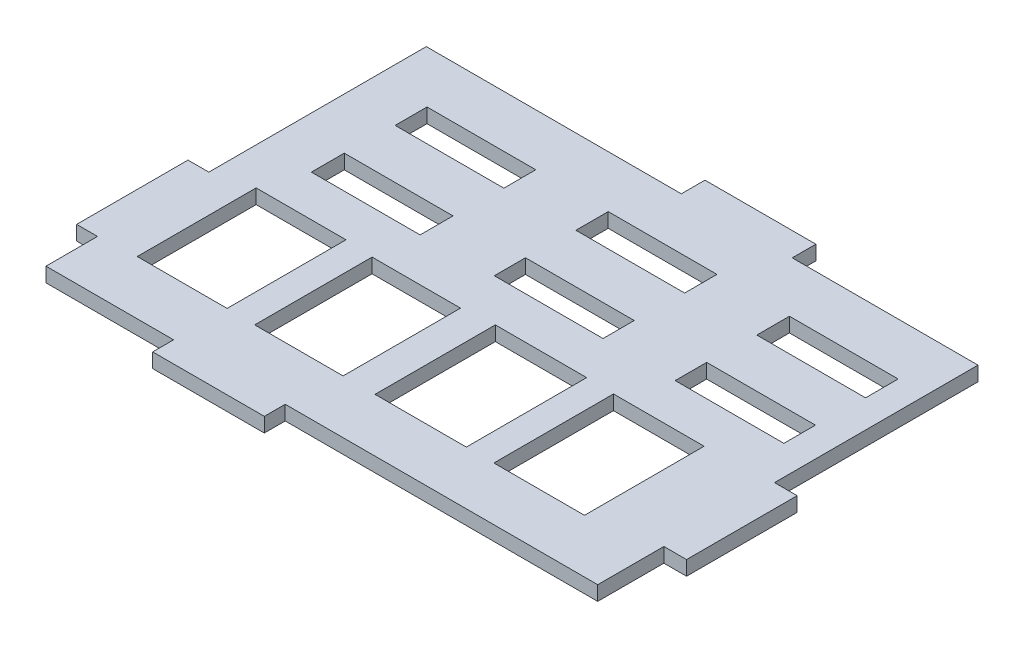
SolidWorks part; units mm, degrees
ref_plane "Front Plane" through (0, 0, 0) normal (0, 0, 1) x (1, 0, 0)
ref_plane "Top Plane" through (0, 0, 0) normal (0, 1, 0) x (1, 0, 0)
ref_plane "Right Plane" through (0, 0, 0) normal (1, 0, 0) x (0, 0, -1)
sketch "Sketch1" plane through (0, 0, 0) normal (0, 1, 0) x (1, 0, 0)
  line L0 (56.9516, 84.2137) -> (56.9516, 75.1881)
  line L1 (56.9516, 141.8209) -> (56.9516, 134.5917)
  line L2 (65.9326, 112.7049) -> (65.9326, 118.4707)
  line L3 (56.9516, 75.1881) -> (79.3066, 75.1881)
  line L4 (153.6179, 141.8209) -> (153.6179, 106.1651)
  line L5 (65.9326, 112.7049) -> (84.9826, 112.7049)
  line L6 (84.9826, 112.7049) -> (84.9826, 118.4707)
  line L7 (65.9326, 118.4707) -> (84.9826, 118.4707)
  line L8 (129.4326, 112.9462) -> (129.4326, 118.4707)
  line L9 (129.4326, 112.9462) -> (148.4826, 112.9462)
  line L10 (148.4826, 112.9462) -> (148.4826, 118.4707)
  line L11 (129.4326, 118.4707) -> (148.4826, 118.4707)
  line L12 (97.6826, 113.0097) -> (97.6826, 118.4707)
  line L13 (97.6826, 113.0097) -> (116.7326, 113.0097)
  line L14 (116.7326, 113.0097) -> (116.7326, 118.4707)
  line L15 (97.6826, 118.4707) -> (116.7326, 118.4707)
  line L16 (56.9516, 116.0497) -> (56.9516, 103.7209)
  line L17 (56.9516, 134.5917) -> (56.9539, 134.5917)
  line L18 (98.8646, 75.1881) -> (153.6179, 75.1881)
  line L19 (56.9516, 116.0497) -> (56.9539, 116.0497)
  line L20 (56.9539, 134.5917) -> (56.9539, 116.0497)
  line L21 (153.6179, 86.7849) -> (153.6179, 75.1881)
  line L22 (79.3066, 75.1881) -> (79.3066, 71.5259)
  line L23 (79.3066, 71.5259) -> (98.8646, 71.5259)
  line L24 (98.8646, 75.1881) -> (98.8646, 71.5259)
  line L25 (153.6179, 106.1651) -> (157.5853, 106.1651)
  line L26 (121.0628, 141.8209) -> (153.6179, 141.8209)
  line L27 (153.6179, 86.7849) -> (157.5853, 86.7849)
  line L28 (157.5853, 106.1651) -> (157.5853, 86.7849)
  line L30 (101.6318, 141.8209) -> (101.6318, 145.9673)
  line L31 (101.6318, 145.9673) -> (121.0628, 145.9673)
  line L32 (121.0628, 141.8209) -> (121.0628, 145.9673)
  line L33 (63.4844, 105.472) -> (79.2324, 105.472)
  line L34 (63.4844, 105.472) -> (63.4844, 84.644)
  line L35 (63.4844, 84.644) -> (79.2324, 84.644)
  line L36 (79.2324, 105.472) -> (79.2324, 84.644)
  line L37 (84.1413, 105.132) -> (99.6353, 105.132)
  line L38 (84.1413, 105.132) -> (84.1413, 84.558)
  line L39 (84.1413, 84.558) -> (99.6353, 84.558)
  line L40 (99.6353, 105.132) -> (99.6353, 84.558)
  line L41 (105.2285, 105.64) -> (121.2305, 105.64)
  line L42 (105.2285, 105.64) -> (105.2285, 84.558)
  line L43 (105.2285, 84.558) -> (121.2305, 84.558)
  line L44 (121.2305, 105.64) -> (121.2305, 84.558)
  line L45 (126.0575, 105.513) -> (141.9325, 105.513)
  line L46 (126.0575, 105.513) -> (126.0575, 84.558)
  line L47 (126.0575, 84.558) -> (141.9325, 84.558)
  line L48 (141.9325, 105.513) -> (141.9325, 84.558)
  line L61 (56.9516, 141.8209) -> (101.6318, 141.8209)
  line L62 (53.2966, 103.7209) -> (53.2966, 84.2137)
  line L65 (53.2966, 103.7209) -> (56.9516, 103.7209)
  line L69 (53.2966, 84.2137) -> (56.9516, 84.2137)
  line L85 (66.178, 127.1328) -> (66.178, 132.7208)
  line L89 (66.178, 127.1328) -> (85.228, 127.1328)
  line L92 (85.228, 127.1328) -> (85.228, 132.7208)
  line L97 (66.178, 132.7208) -> (85.228, 132.7208)
  line L100 (129.678, 127.0058) -> (129.678, 132.7208)
  line L101 (129.678, 127.0058) -> (148.728, 127.0058)
  line L102 (148.728, 127.0058) -> (148.728, 132.7208)
  line L103 (129.678, 132.7208) -> (148.728, 132.7208)
  line L104 (97.928, 127.0566) -> (97.928, 132.7208)
  line L105 (97.928, 127.0566) -> (116.978, 127.0566)
  line L106 (116.978, 127.0566) -> (116.978, 132.7208)
  line L107 (97.928, 132.7208) -> (116.978, 132.7208)
  dimension "D3" = 5.461
  dimension "D4" = 5.5245
  dimension "D1" = 5.7658
  dimension "D5" = 15.748
  dimension "D9" = 19.558
  dimension "D10" = 19.3802
  dimension "D11" = 19.431
  dimension "D12" = 20.828
  dimension "D13" = 20.574
  dimension "D14" = 15.494
  dimension "D15" = 16.002
  dimension "D16" = 21.082
  dimension "D17" = 20.955
  dimension "D18" = 15.875
  dimension "D27" = 5.588
  dimension "D68" = 38.1
  dimension "D69" = 19.5072
  dimension "D77" = 5.6642
  dimension "D78" = 5.715
  dimension "D80" = 19.05
  dimension "D82" = 19.05
  dimension "D83" = 12.7
  dimension "D84" = 12.7
extrude "Boss-Extrude1" add sketch "Sketch1" along normal blind 2.54
